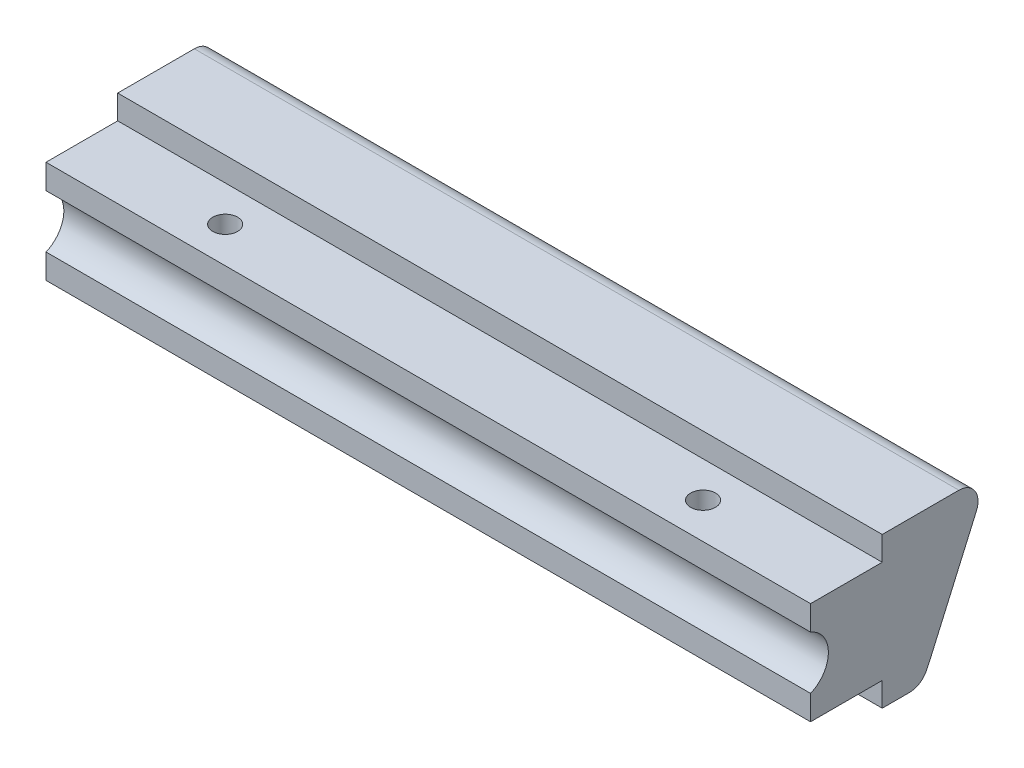
SolidWorks part; units mm, degrees
ref_plane "Front Plane" through (0, 0, 0) normal (0, 0, 1) x (1, 0, 0)
ref_plane "Top Plane" through (0, 0, 0) normal (0, 1, 0) x (1, 0, 0)
ref_plane "Right Plane" through (0, 0, 0) normal (1, 0, 0) x (0, 0, -1)
sketch "Sketch1" plane through (0, 0, 0) normal (1, 0, 0) x (0, 0, -1)
  line L0 (0, 16.7996) -> (0, 3.2004)
  line L1 (0, 20) -> (14.605, 20) construction
  line L2 (0, 20) -> (0, 0) construction
  line L3 (0, 0) -> (14.605, 0) construction
  line L4 (14.605, 20) -> (14.605, 0) construction
  line L5 (0, 20) -> (14.605, 20) construction
  line L6 (0, 20) -> (0, 16.7996) construction
  line L9 (0, 3.2004) -> (9.525, 3.2004)
  line L10 (0, 3.2004) -> (0, 0) construction
  line L11 (0, 0) -> (14.605, 0) construction
  line L14 (23.6039, 20) -> (15.8687, 2.3944)
  line L15 (14.605, 0) -> (9.525, 0)
  line L16 (9.525, 3.2004) -> (9.525, 0)
  line L17 (23.6039, 20) -> (9.525, 20)
  line L18 (9.525, 20) -> (9.525, 16.7996)
  line L19 (9.525, 16.7996) -> (0, 16.7996)
  arc A2 (15.8687, 2.3944) -> (14.605, 0) centre (-1.4419, 10) cw
  dimension "D4" = 9.525
  dimension "D5" = 18.9078
  dimension "D1" = 20
  dimension "D2" = 2.3944
  dimension "D3" = 3.2004
  dimension "D6" = 113.719
  dimension "D7" = 5.08
extrude "Boss-Extrude1" add sketch "Sketch1" along normal blind 101.6
sketch "Sketch4" plane through (0, 0, 0) normal (-1, 0, 0) x (0, 0, 1)
  line L1 (0, 13.5263) -> (0, 6.4737)
  line L2 (-19.2103, 10) -> (1.4427, 10) construction
  line L3 (0, 3.2004) -> (-9.525, 3.2004) construction
  line L4 (0, 16.7996) -> (0, 3.2004) construction
  line L5 (-15.8687, 2.3944) -> (-23.6039, 20) construction
  arc A0 (0, 13.5263) -> (0, 6.4737) centre (1.4427, 10) ccw
  point P3 (0, 10)
  dimension "D1" = 3.81
  dimension "D2" = 1.4427
extrude "Cut-Extrude2" cut sketch "Sketch4" against normal up to surface (101.6 mm away) up to face at (101.6, 9.1524, -10.2467)
sketch "Sketch5" plane through (0, 16.7996, 0) normal (0, 1, 0) x (1, 0, 0)
  line L0 (50.8, 9.525) -> (50.8, 0) construction
  line L1 (19.05, 4.7625) -> (82.55, 4.7625) construction
  line L2 (101.6, 9.525) -> (0, 9.525) construction
  line L3 (101.6, 0) -> (0, 0) construction
  circle A4 centre (19.05, 4.7625) radius 1.651
  circle A5 centre (82.55, 4.7625) radius 1.651
  point P8 (50.8, 4.7625)
  dimension "D1" = 63.5
  dimension "D2" = 3.302
extrude "Cut-Extrude3" cut sketch "Sketch5" against normal up to surface (13.5992 mm away) up to face at (50.8, 3.2004, -4.7625)
fillet "Fillet1" radius 2.54 2 edges at (50.8, 0, -14.605) (50.8, 20, -23.6039)
